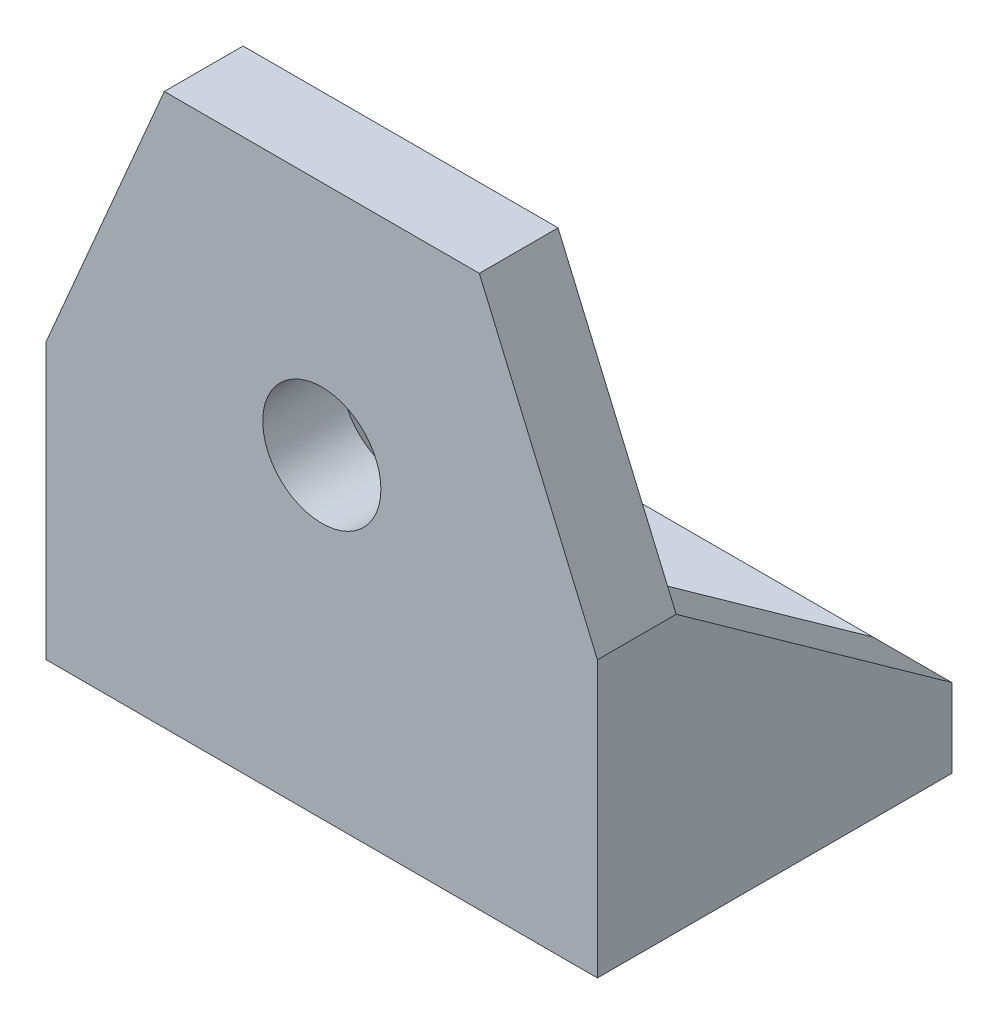
SolidWorks part; units mm, degrees
ref_plane "Front Plane" through (0, 0, 0) normal (0, 0, 1) x (1, 0, 0)
ref_plane "Top Plane" through (0, 0, 0) normal (0, 1, 0) x (1, 0, 0)
ref_plane "Right Plane" through (0, 0, 0) normal (1, 0, 0) x (0, 0, -1)
sketch "Sketch1" plane through (0, 0, 0) normal (0, 1, 0) x (1, 0, 0)
  line L1 (-7, 4.5) -> (7, 4.5)
  line L2 (-7, 4.5) -> (-7, -4.5)
  line L3 (-7, -4.5) -> (7, -4.5)
  line L4 (7, 4.5) -> (7, -4.5)
  line L5 (-7, 4.5) -> (7, -4.5) construction
  line L6 (-7, -4.5) -> (7, 4.5) construction
  point P0 (0, 0)
  dimension "D1" = 14
  dimension "D2" = 9
extrude "Boss-Extrude1" add sketch "Sketch1" along normal blind 2
sketch "Sketch2" plane through (0, 2, 0) normal (0, 1, 0) x (1, 0, 0)
  line L0 (0, 4.5) -> (0, -4.5) construction
  line L1 (7, 4.5) -> (-7, 4.5) construction
  line L2 (-7, -4.5) -> (7, -4.5) construction
  circle A0 centre (-3, 1) radius 1.25
  circle A1 centre (3, 1) radius 1.25
  dimension "D1" = 2.5
  dimension "D2" = 2.5
  dimension "D3" = 6
  dimension "D4" = 3
  dimension "D5" = 3.5
extrude "Cut-Extrude1" cut sketch "Sketch2" against normal blind 2
sketch "Sketch3" plane through (0, 2, 0) normal (0, 1, 0) x (1, 0, 0)
  line L0 (7, -4.5) -> (7, 4.5) construction
  line L1 (-7, -4.5) -> (7, -4.5)
  line L2 (-7, -4.5) -> (-7, -2.5)
  line L3 (-7, -2.5) -> (7, -2.5)
  line L4 (7, -4.5) -> (7, -2.5)
  dimension "D1" = 2
extrude "Boss-Extrude2" add sketch "Sketch3" along normal blind 12
sketch "Sketch4" plane through (0, 0, 4.5) normal (0, 0, 1) x (1, 0, 0)
  line L0 (-7, 7) -> (-4, 14)
  line L1 (-7, 14) -> (-7, 0) construction
  line L2 (-7, 14) -> (7, 14) construction
  line L3 (4, 14) -> (7, 7)
  line L4 (7, 14) -> (7, 0) construction
  line L5 (7, 7) -> (7, 14)
  line L6 (7, 14) -> (4, 14)
  line L7 (-7, 7) -> (-7, 14)
  line L8 (-7, 14) -> (-4, 14)
  line L9 (0, 14) -> (0, 0) construction
  line L10 (-7, 0) -> (7, 0) construction
  dimension "D1" = 7
  dimension "D2" = 7
  dimension "D3" = 8
  dimension "D4" = 4
extrude "Cut-Extrude2" cut sketch "Sketch4" against normal blind 12
sketch "Sketch5" plane through (0, 0, 2.5) normal (0, 0, -1) x (-1, 0, 0)
  line L0 (-7, 2) -> (7, 2) construction
  line L1 (-7, 7) -> (-5, 7)
  line L2 (-7, 7) -> (-7, 2)
  line L3 (-7, 2) -> (-5, 2)
  line L4 (-5, 7) -> (-5, 2)
  line L5 (-7, 2) -> (7, 2) construction
  line L6 (7, 7) -> (5, 7)
  line L7 (7, 7) -> (7, 2)
  line L8 (7, 2) -> (5, 2)
  line L9 (5, 7) -> (5, 2)
  dimension "D1" = 2
  dimension "D2" = 2
extrude "Boss-Extrude3" add sketch "Sketch5" along normal up to surface (7 mm away) up to face at (0, 1, -4.5)
sketch "Sketch6" plane through (7, 0, 0) normal (1, 0, 0) x (0, 0, -1)
  line L0 (-2.5, 7) -> (4.5, 2)
  line L1 (4.5, 7) -> (4.5, 0) construction
  line L2 (4.5, 2) -> (4.5, 7)
  line L3 (4.5, 7) -> (-2.5, 7)
  dimension "D1" = 2
extrude "Cut-Extrude3" cut sketch "Sketch6" against normal up to surface (14 mm away) up to face at (-7, 4.2, 0.5)
sketch "Sketch7" plane through (0, 0, 4.5) normal (0, 0, 1) x (1, 0, 0)
  line L0 (0, 14) -> (0, 0) construction
  line L1 (-4, 14) -> (4, 14) construction
  circle A0 centre (0, 8) radius 1.5
  dimension "D1" = 3
  dimension "D2" = 6
extrude "Cut-Extrude4" cut sketch "Sketch7" against normal up to surface (2 mm away) up to face at (0, 7.5, 2.5)
